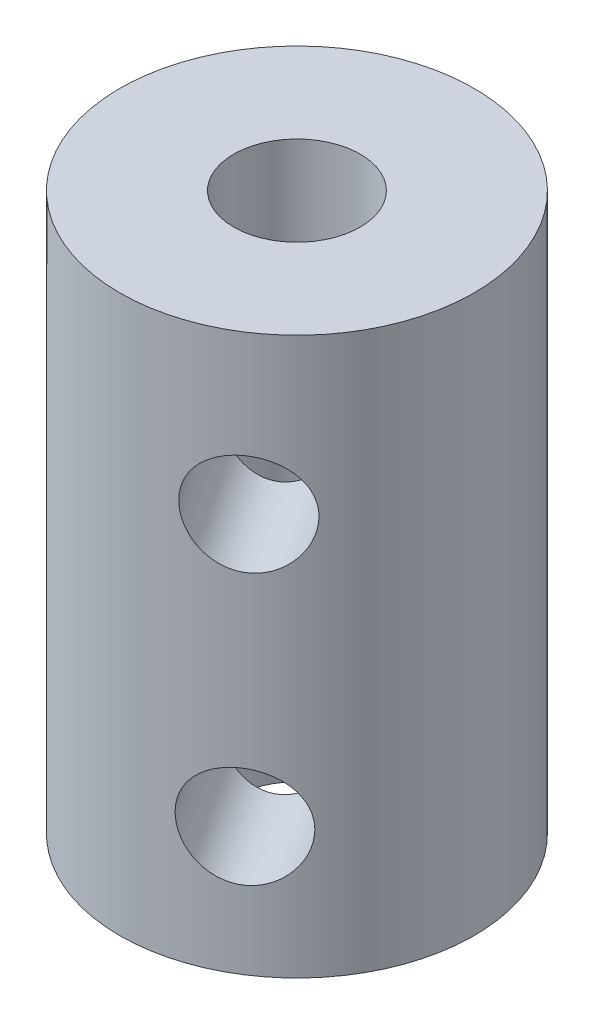
SolidWorks part; units mm, degrees
ref_plane "前视基准面" through (0, 0, 0) normal (0, 0, 1) x (1, 0, 0)
ref_plane "上视基准面" through (0, 0, 0) normal (0, 1, 0) x (1, 0, 0)
ref_plane "右视基准面" through (0, 0, 0) normal (1, 0, 0) x (0, 0, -1)
sketch "草图1" plane through (0, 0, 0) normal (0, 1, 0) x (1, 0, 0)
  circle A0 centre (0, 0) radius 2.5
  circle A1 centre (0, 0) radius 7
  dimension "D1" = 5
  dimension "D2" = 14
extrude "凸台-拉伸1" add sketch "草图1" along normal blind 22
hole_wizard "大小mm 暗销孔1" positions "3D草图2" profile "草图3" hole size "Ø4.0" standard "ISO"
sketch3d "3D草图2"
  point P0 (3.8578, 15.7711, 5.841)
  point P2 (3.7603, 5.0671, 5.9042)
sketch "草图3" plane through (3.8578, 15.7711, 5.841) normal (0, 1, 0) x (0.8344, 0, -0.5511)
  line L0 (0, 0) -> (0, 4.5)
  line L1 (0, 4.5) -> (2, 4.5)
  line L2 (2, 4.5) -> (2, 0)
  line L5 (2, 0) -> (0, 0)
  line L11 (0, -6.35) -> (0, 107.95) construction
  dimension "通孔孔直径" = 4
  dimension "通孔孔深度" = 4.5
